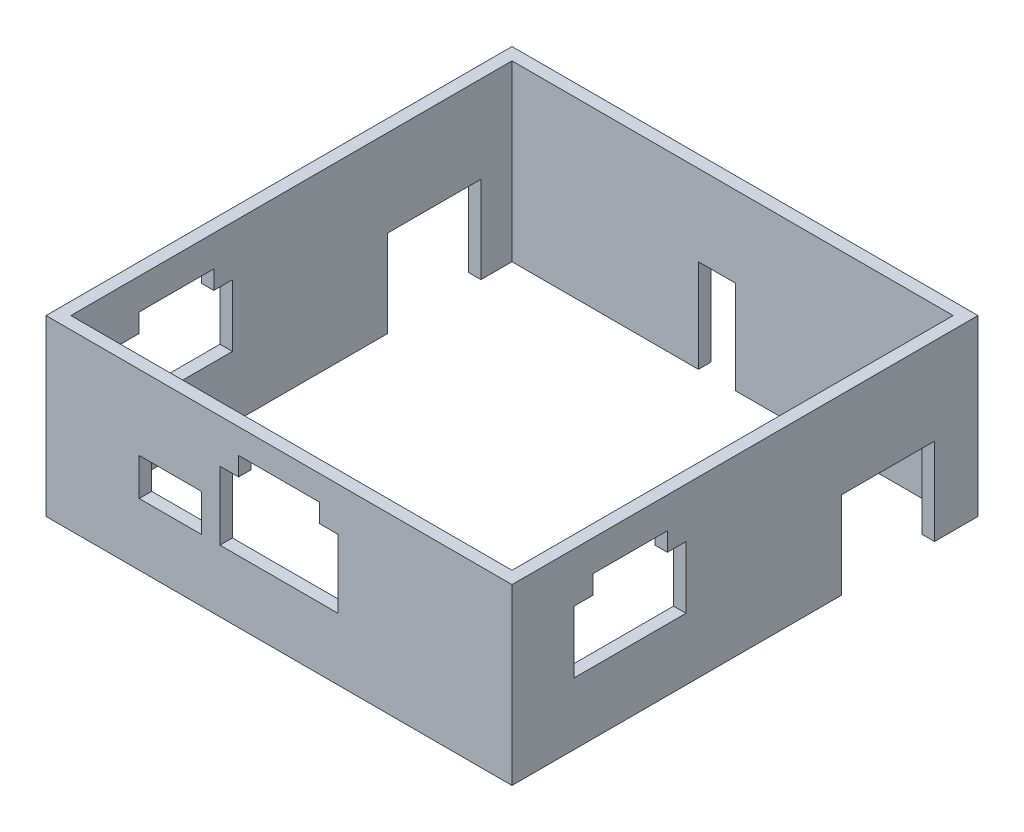
SolidWorks part; units mm, degrees
ref_plane "Front Plane" through (0, 0, 0) normal (0, 0, 1) x (1, 0, 0)
ref_plane "Top Plane" through (0, 0, 0) normal (0, 1, 0) x (1, 0, 0)
ref_plane "Right Plane" through (0, 0, 0) normal (1, 0, 0) x (0, 0, -1)
sketch "Sketch1" plane through (0, 0, 0) normal (0, 1, 0) x (1, 0, 0)
  line L1 (-37.5, 37.5) -> (37.5, 37.5)
  line L2 (-37.5, 37.5) -> (-37.5, -37.5)
  line L3 (-37.5, -37.5) -> (37.5, -37.5)
  line L4 (37.5, 37.5) -> (37.5, -37.5)
  line L5 (-37.5, 37.5) -> (37.5, -37.5) construction
  line L6 (-37.5, -37.5) -> (37.5, 37.5) construction
  point P0 (0, 0)
  dimension "D1" = 75
  dimension "D2" = 75
extrude "Boss-Extrude1" add sketch "Sketch1" along normal blind 28
sketch "Sketch2" plane through (0, 28, 0) normal (0, 1, 0) x (1, 0, 0)
  line L8 (35.5, -35.5) -> (35.5, 35.5)
  line L9 (35.5, 35.5) -> (-35.5, 35.5)
  line L10 (-35.5, 35.5) -> (-35.5, -35.5)
  line L11 (-35.5, -35.5) -> (35.5, -35.5)
  line L12 (35.5, -35.5) -> (35.5, 35.5)
  line L13 (35.5, 35.5) -> (-35.5, 35.5)
  line L14 (-35.5, 35.5) -> (-35.5, -35.5)
  line L15 (-35.5, -35.5) -> (35.5, -35.5)
  dimension "D1" = 2
extrude "Cut-Extrude1" cut sketch "Sketch2" against normal through all
sketch "Sketch3" plane through (0, 0, 37.5) normal (0, 0, 1) x (1, 0, 0)
  line L0 (-37.5, 28) -> (-37.5, 0) construction
  line L1 (-22.5, 16) -> (-12.5, 16)
  line L2 (-22.5, 16) -> (-22.5, 10)
  line L3 (-22.5, 10) -> (-12.5, 10)
  line L4 (-12.5, 16) -> (-12.5, 10)
  line L5 (-22.5, 16) -> (-12.5, 10) construction
  line L6 (-22.5, 10) -> (-12.5, 16) construction
  line L7 (-6.5, 24) -> (6.5, 24)
  line L8 (-9.5, 21) -> (-9.5, 10)
  line L9 (-9.5, 10) -> (9.5, 10)
  line L10 (9.5, 21) -> (9.5, 10)
  line L11 (-6.5, 21.7895) -> (9.5, 10) construction
  line L12 (-9.5, 10) -> (6.5, 21.7895) construction
  line L13 (37.5, 28) -> (37.5, 0) construction
  line L14 (-37.5, 0) -> (37.5, 0) construction
  line L18 (-9.5, 21) -> (-6.5, 21)
  line L19 (-6.5, 24) -> (-6.5, 21)
  line L22 (9.5, 21) -> (6.5, 21)
  line L23 (6.5, 24) -> (6.5, 21)
  point P0 (-17.5, 13)
  point P5 (0, 17)
  dimension "D1" = 10
  dimension "D2" = 6
  dimension "D3" = 28
  dimension "D4" = 28
  dimension "D5" = 10
  dimension "D6" = 14
  dimension "D7" = 15
  dimension "D8" = 10
  dimension "D9" = 3
  dimension "D10" = 3
  dimension "D11" = 3
  dimension "D12" = 3
extrude "Cut-Extrude2" cut sketch "Sketch3" against normal blind 2
sketch "Sketch4" plane through (-37.5, 0, 0) normal (-1, 0, 0) x (0, 0, 1)
  line L0 (-37.5, 0) -> (37.5, 0) construction
  line L1 (12.5, 23) -> (24.5, 23)
  line L2 (9.5, 20) -> (9.5, 10)
  line L3 (9.5, 10) -> (27.5, 10)
  line L4 (27.5, 20) -> (27.5, 10)
  line L5 (12.5, 21.6667) -> (27.5, 10) construction
  line L6 (9.5, 10) -> (24.5, 21.6667) construction
  line L7 (-30.5, 14) -> (-15.5, 14)
  line L8 (-30.5, 14) -> (-30.5, 0)
  line L9 (-30.5, 0) -> (-15.5, 0)
  line L10 (-15.5, 14) -> (-15.5, 0)
  line L11 (-30.5, 14) -> (-15.5, 0) construction
  line L12 (-30.5, 0) -> (-15.5, 14) construction
  line L13 (-37.5, 28) -> (-37.5, 0) construction
  line L14 (37.5, 28) -> (37.5, 0) construction
  line L18 (9.5, 20) -> (12.5, 20)
  line L19 (12.5, 23) -> (12.5, 20)
  line L22 (27.5, 20) -> (24.5, 20)
  line L23 (24.5, 23) -> (24.5, 20)
  point P0 (18.5, 17)
  point P5 (-23, 7)
  dimension "D1" = 7
  dimension "D2" = 14
  dimension "D3" = 15
  dimension "D4" = 18
  dimension "D5" = 13
  dimension "D6" = 10
  dimension "D7" = 10
  dimension "D8" = 3
  dimension "D9" = 3
  dimension "D10" = 3
  dimension "D11" = 3
extrude "Cut-Extrude3" cut sketch "Sketch4" against normal through all
sketch "Sketch5" plane through (0, 0, -37.5) normal (0, 0, -1) x (-1, 0, 0)
  line L0 (-37.5, 0) -> (37.5, 0) construction
  line L1 (-0.5, 15) -> (5.5, 15)
  line L2 (-0.5, 15) -> (-0.5, 0)
  line L3 (-0.5, 0) -> (5.5, 0)
  line L4 (5.5, 15) -> (5.5, 0)
  line L5 (-0.5, 15) -> (5.5, 0) construction
  line L6 (-0.5, 0) -> (5.5, 15) construction
  line L7 (-37.5, 28) -> (-37.5, 0) construction
  line L8 (37.5, 28) -> (37.5, 0) construction
  point P0 (2.5, 7.5)
  dimension "D1" = 37
  dimension "D2" = 32
  dimension "D3" = 15
extrude "Cut-Extrude4" cut sketch "Sketch5" against normal blind 2
